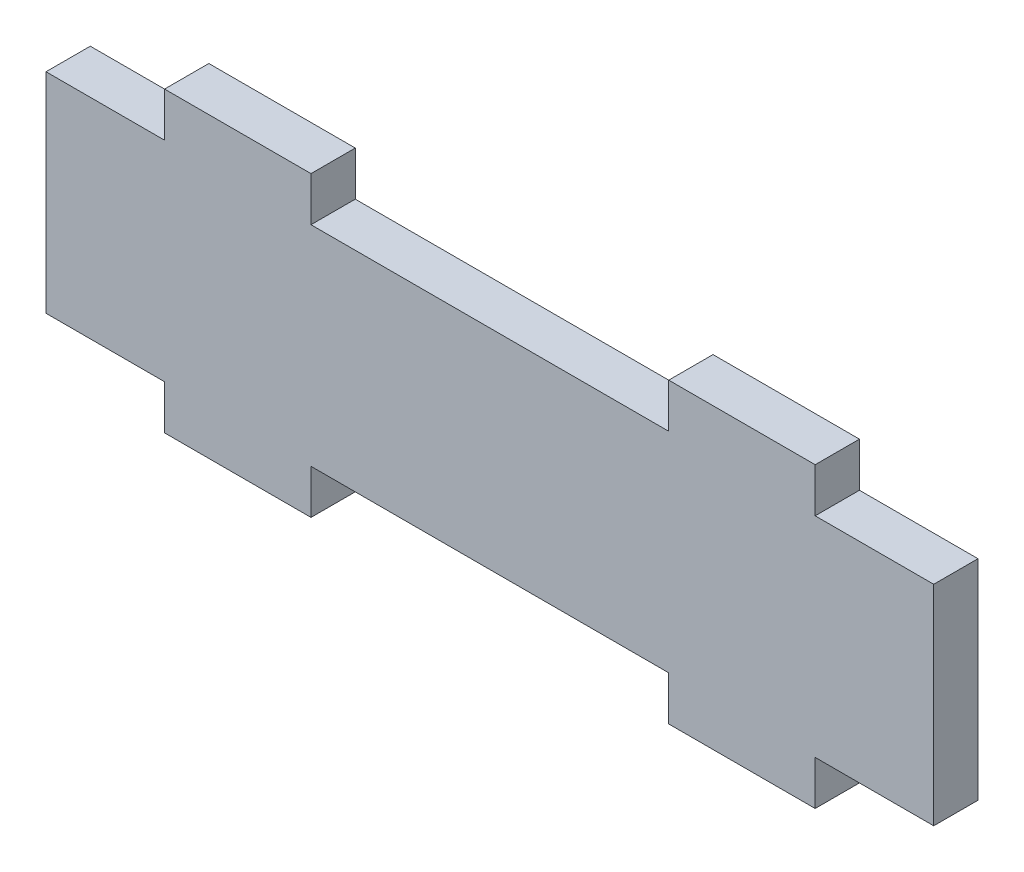
SolidWorks part; units mm, degrees
ref_plane "Front Plane" through (0, 0, 0) normal (0, 0, 1) x (1, 0, 0)
ref_plane "Top Plane" through (0, 0, 0) normal (0, 1, 0) x (1, 0, 0)
ref_plane "Right Plane" through (0, 0, 0) normal (1, 0, 0) x (0, 0, -1)
sketch "Sketch1" plane through (0, 0, 0) normal (0, 0, 1) x (1, 0, 0)
  line L0 (-31.825, 10.675) -> (31.825, 10.675) construction
  line L1 (-31.825, -7.5) -> (31.825, -7.5)
  line L2 (-31.825, -7.5) -> (-31.825, 7.5)
  line L3 (-31.825, 7.5) -> (31.825, 7.5)
  line L4 (31.825, -7.5) -> (31.825, 7.5)
  line L5 (-31.825, -7.5) -> (31.825, 7.5) construction
  line L6 (-31.825, 7.5) -> (31.825, -7.5) construction
  line L7 (-31.825, -10.675) -> (31.825, -10.675) construction
  line L8 (-4.325, -7.5) -> (-4.325, 7.5) construction
  line L9 (-31.825, 0) -> (-4.325, 0) construction
  line L10 (-18.075, 0) -> (-18.075, 7.5) construction
  line L11 (0, 0) -> (0, 7.5) construction
  line L12 (-23.325, 4.325) -> (-12.825, 4.325)
  line L13 (-23.325, 4.325) -> (-23.325, 10.675)
  line L14 (-23.325, 10.675) -> (-12.825, 10.675)
  line L15 (-12.825, 4.325) -> (-12.825, 10.675)
  line L16 (-23.325, 4.325) -> (-12.825, 10.675) construction
  line L17 (-23.325, 10.675) -> (-12.825, 4.325) construction
  line L18 (23.325, 10.675) -> (12.825, 4.325) construction
  line L19 (23.325, 4.325) -> (12.825, 10.675) construction
  line L20 (12.825, 4.325) -> (12.825, 10.675)
  line L21 (23.325, 10.675) -> (12.825, 10.675)
  line L22 (23.325, 4.325) -> (23.325, 10.675)
  line L23 (23.325, 4.325) -> (12.825, 4.325)
  line L24 (23.325, -4.325) -> (12.825, -10.675) construction
  line L25 (23.325, -10.675) -> (12.825, -4.325) construction
  line L26 (23.325, -4.325) -> (12.825, -4.325)
  line L27 (23.325, -4.325) -> (23.325, -10.675)
  line L28 (23.325, -10.675) -> (12.825, -10.675)
  line L29 (12.825, -4.325) -> (12.825, -10.675)
  line L30 (-23.325, -10.675) -> (-12.825, -4.325) construction
  line L31 (-23.325, -4.325) -> (-12.825, -10.675) construction
  line L32 (-12.825, -4.325) -> (-12.825, -10.675)
  line L33 (-23.325, -10.675) -> (-12.825, -10.675)
  line L34 (-23.325, -4.325) -> (-23.325, -10.675)
  line L35 (-23.325, -4.325) -> (-12.825, -4.325)
  point P0 (0, 0)
  dimension "D1" = 15
  dimension "D2" = 63.65
  dimension "D6" = 10.5
  dimension "D3" = 3.175
  dimension "D4" = 3.175
  dimension "D5" = 27.5
extrude "Boss-Extrude1" add sketch "Sketch1" along normal blind 3.175 contours L34 L35 L32 L1 L29 L26 L27 L4 L3 L22 L23 L20 L15 L12 L13 L2 | L12 L15 L3 L13 | L1 L34 L33 L32 | L35 L34 L1 L32 | L3 L22 L21 L20 | L26 L29 L1 L27 | L1 L29 L28 L27
